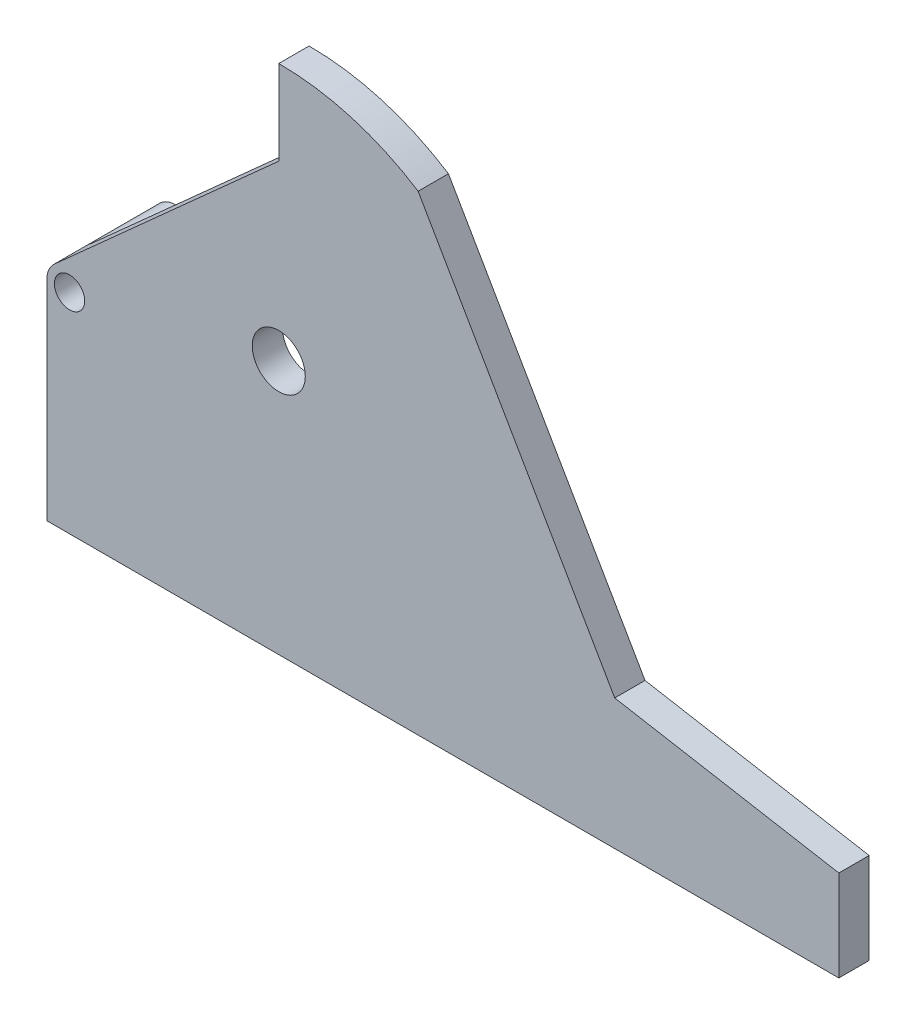
SolidWorks part; units mm, degrees
ref_plane "Front Plane" through (0, 0, 0) normal (0, 0, 1) x (1, 0, 0)
ref_plane "Top Plane" through (0, 0, 0) normal (0, 1, 0) x (1, 0, 0)
ref_plane "Right Plane" through (0, 0, 0) normal (1, 0, 0) x (0, 0, -1)
sketch "Sketch1" plane through (0, 0, 0) normal (0, 0, 1) x (1, 0, 0)
  line L0 (-54.9958, 0) -> (67.63, 0) construction
  line L1 (0, 23.262) -> (0, -27.492) construction
  line L2 (0, 0) -> (522.5, 0)
  line L3 (0, 0) -> (0, 138)
  line L8 (4.9848, 149.1667) -> (129.7305, 261.0488)
  line L10 (129.7305, 261.0488) -> (153, 281.9188)
  line L11 (153, 281.9188) -> (153, 337.7402)
  line L13 (244.94, 310.7333) -> (374.6494, 86.07)
  line L14 (522.5, 0) -> (522.5, 60)
  line L15 (522.5, 60) -> (374.6494, 86.07)
  circle A0 centre (15, 138) radius 15
  circle A2 centre (15, 138) radius 10
  arc A4 (244.94, 310.7333) -> (153, 337.7402) centre (153, 167.7402) ccw
  circle A5 centre (153, 167.7402) radius 17.5
  point P15 (153, 167.7402)
  dimension "D3" = 30
  dimension "D2" = 170
extrude "Boss-Extrude1" add sketch "Sketch1" along normal blind 20 contours L13 A4 L11 L10 L8 A0 L3 L2 L14 L15 A5 | A2
sketch "Sketch2" plane through (0, 0, 20) normal (0, 0, 1) x (1, 0, 0)
  circle A0 centre (15, 138) radius 10
  circle A1 centre (15, 138) radius 15
extrude "Boss-Extrude2" add sketch "Sketch2" against normal blind 70
